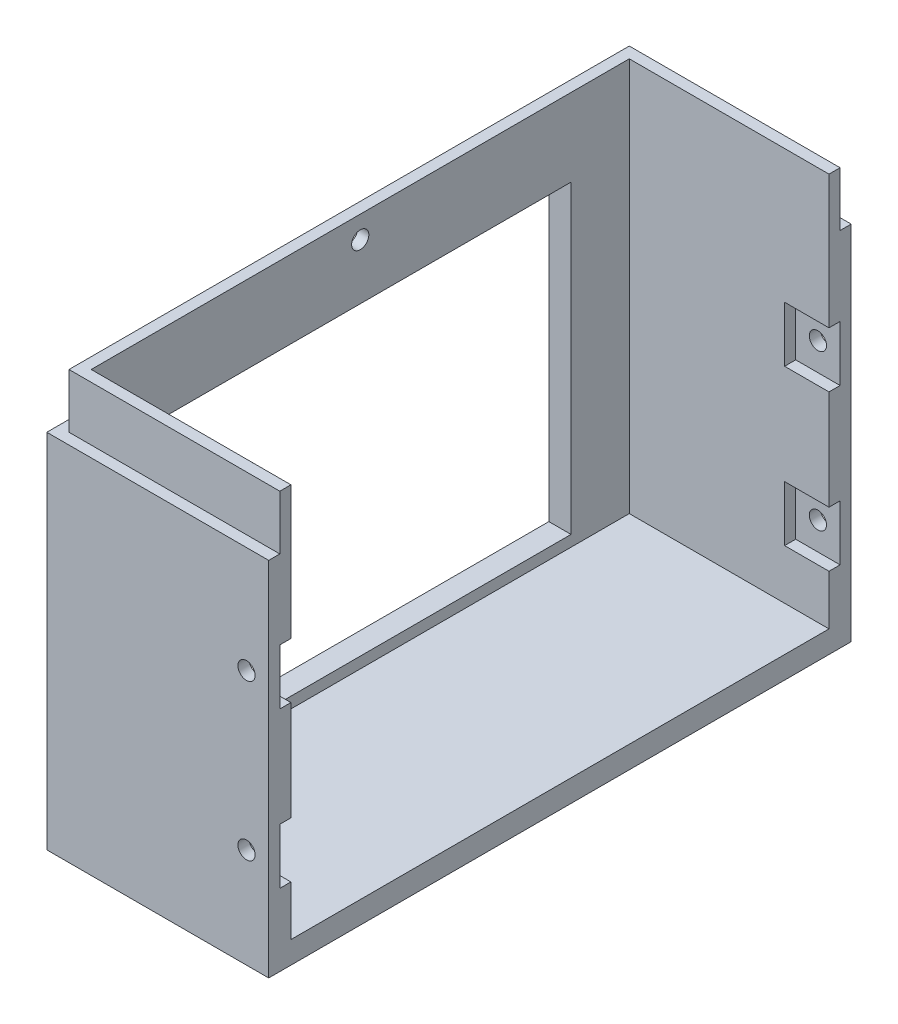
SolidWorks part; units mm, degrees
ref_plane "Front Plane" through (0, 0, 0) normal (0, 0, 1) x (1, 0, 0)
ref_plane "Top Plane" through (0, 0, 0) normal (0, 1, 0) x (1, 0, 0)
ref_plane "Right Plane" through (0, 0, 0) normal (1, 0, 0) x (0, 0, -1)
sketch "Sketch1" plane through (0, 0, 0) normal (0, 1, 0) x (1, 0, 0)
  line L1 (-20, 52.5) -> (20, 52.5)
  line L2 (-20, 52.5) -> (-20, -52.5)
  line L3 (-20, -52.5) -> (20, -52.5)
  line L4 (20, 52.5) -> (20, -52.5)
  line L5 (-20, 52.5) -> (20, -52.5) construction
  line L6 (-20, -52.5) -> (20, 52.5) construction
  point P0 (0, 0)
  dimension "D1" = 105
  dimension "D2" = 40
extrude "Boss-Extrude3" add sketch "Sketch1" along normal blind 75
sketch "Sketch4" plane through (20, 0, 0) normal (1, 0, 0) x (0, 0, -1)
  line L0 (-52.5, 75) -> (52.5, 75) construction
  line L1 (-48.5, 75) -> (48.5, 75)
  line L2 (-48.5, 75) -> (-48.5, 4)
  line L3 (-48.5, 4) -> (48.5, 4)
  line L4 (48.5, 75) -> (48.5, 4)
  line L5 (-52.5, 75) -> (-52.5, 0) construction
  line L6 (-52.5, 0) -> (52.5, 0) construction
  line L7 (52.5, 75) -> (52.5, 0) construction
  dimension "D1" = 4
  dimension "D2" = 4
  dimension "D3" = 4
extrude "Cut-Extrude2" cut sketch "Sketch4" against normal blind 36
sketch "Sketch5" plane through (0, 0, 52.5) normal (0, 0, 1) x (1, 0, 0)
  line L0 (-20, 75) -> (-20, 0) construction
  line L1 (20, 75) -> (-20, 75)
  line L2 (20, 75) -> (20, 65.2)
  line L3 (20, 65.2) -> (-20, 65.2)
  line L4 (-20, 75) -> (-20, 65.2)
  dimension "D1" = 9.8
extrude "Cut-Extrude3" cut sketch "Sketch5" against normal blind 2
sketch "Sketch6" plane through (0, 0, -52.5) normal (0, 0, -1) x (-1, 0, 0)
  line L0 (20, 75) -> (20, 0) construction
  line L1 (-20, 75) -> (20, 75)
  line L2 (-20, 75) -> (-20, 65.2)
  line L3 (-20, 65.2) -> (20, 65.2)
  line L4 (20, 75) -> (20, 65.2)
  dimension "D1" = 9.8
extrude "Cut-Extrude4" cut sketch "Sketch6" against normal blind 2
sketch "Sketch7" plane through (-20, 0, 0) normal (-1, 0, 0) x (0, 0, 1)
  line L1 (-50.5, 75) -> (50.5, 75)
  line L2 (-50.5, 75) -> (-50.5, 65.2)
  line L3 (-50.5, 65.2) -> (50.5, 65.2)
  line L4 (50.5, 75) -> (50.5, 65.2)
extrude "Cut-Extrude5" cut sketch "Sketch7" against normal blind 2
sketch "Sketch8" plane through (0, 0, 48.5) normal (0, 0, -1) x (-1, 0, 0)
  line L0 (-20, 75) -> (-20, 4) construction
  line L1 (16, 4) -> (-20, 4) construction
  circle A0 centre (-16, 18) radius 1.55
  circle A1 centre (-16, 46) radius 1.55
  dimension "D1" = 3.1
  dimension "D2" = 3.1
  dimension "D5" = 14
  dimension "D6" = 28
  dimension "D3" = 4
  dimension "D4" = 4
extrude "Cut-Extrude6" cut sketch "Sketch8" against normal through all and the other way through all
sketch "Sketch9" plane through (0, 0, 48.5) normal (0, 0, -1) x (-1, 0, 0)
  line L0 (-20, 75) -> (-20, 4) construction
  line L1 (-12, 23) -> (-20, 23)
  line L2 (-12, 23) -> (-12, 13)
  line L3 (-12, 13) -> (-20, 13)
  line L4 (-20, 23) -> (-20, 13)
  line L5 (-12, 23) -> (-20, 13) construction
  line L6 (-12, 13) -> (-20, 23) construction
  line L8 (-20, 51) -> (-12, 51)
  line L9 (-20, 51) -> (-20, 41)
  line L10 (-20, 41) -> (-12, 41)
  line L11 (-12, 51) -> (-12, 41)
  line L12 (-20, 51) -> (-12, 41) construction
  line L13 (-20, 41) -> (-12, 51) construction
  point P0 (-16, 18)
  point P8 (-16, 46)
  dimension "D1" = 10
  dimension "D2" = 10
extrude "Cut-Extrude7" cut sketch "Sketch9" against normal blind 2
sketch "Sketch10" plane through (-18, 0, 0) normal (-1, 0, 0) x (0, 0, 1)
  line L0 (50.5, 75) -> (-50.5, 75) construction
  circle A0 centre (0, 71) radius 1.55
  dimension "D1" = 3.1
  dimension "D2" = 4
extrude "Cut-Extrude8" cut sketch "Sketch10" against normal blind 2
sketch "Sketch11" plane through (0, 0, -48.5) normal (0, 0, 1) x (1, 0, 0)
  line L0 (20, 4) -> (20, 75) construction
  line L1 (12, 51) -> (20, 51)
  line L2 (12, 51) -> (12, 41)
  line L3 (12, 41) -> (20, 41)
  line L4 (20, 51) -> (20, 41)
  line L5 (12, 51) -> (20, 41) construction
  line L6 (12, 41) -> (20, 51) construction
  line L8 (12, 23) -> (20, 23)
  line L9 (12, 23) -> (12, 13)
  line L10 (12, 13) -> (20, 13)
  line L11 (20, 23) -> (20, 13)
  line L12 (12, 23) -> (20, 13) construction
  line L13 (12, 13) -> (20, 23) construction
  point P0 (16, 46)
  point P8 (16, 18)
  dimension "D1" = 8
  dimension "D2" = 10
  dimension "D3" = 10
extrude "Cut-Extrude9" cut sketch "Sketch11" against normal blind 2
sketch "Sketch12" plane through (-20, 0, 0) normal (-1, 0, 0) x (0, 0, 1)
  line L0 (-52.5, 65.2) -> (-52.5, 0) construction
  line L1 (-38, 61) -> (38, 61)
  line L2 (-38, 61) -> (-38, 6)
  line L3 (-38, 6) -> (38, 6)
  line L4 (38, 61) -> (38, 6)
  line L5 (-38, 61) -> (38, 6) construction
  line L6 (-38, 6) -> (38, 61) construction
  line L7 (-52.5, 0) -> (52.5, 0) construction
  point P0 (0, 33.5)
  dimension "D1" = 76
  dimension "D2" = 55
  dimension "D3" = 52.5
  dimension "D4" = 6
extrude "Cut-Extrude10" cut sketch "Sketch12" against normal up to next
